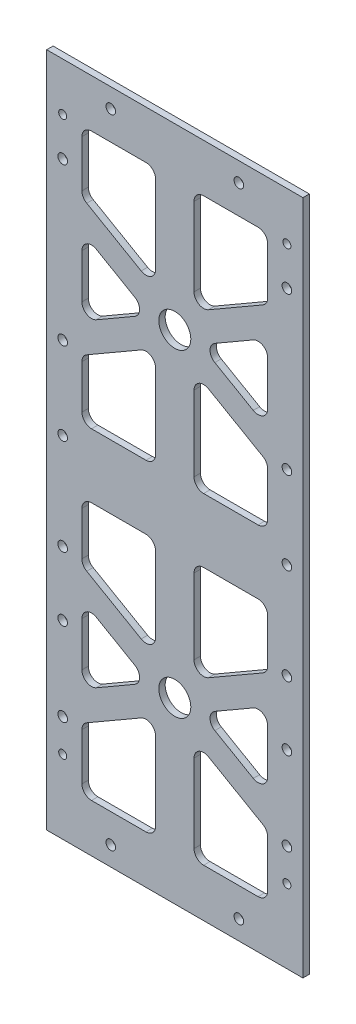
SolidWorks part; units mm, degrees
material "6061-T6 (SS)"
ref_plane "Front Plane" through (0, 0, 0) normal (0, 0, 1) x (1, 0, 0)
ref_plane "Top Plane" through (0, 0, 0) normal (0, 1, 0) x (1, 0, 0)
ref_plane "Right Plane" through (0, 0, 0) normal (1, 0, 0) x (0, 0, -1)
sketch "Sketch1" plane through (0, 0, 0) normal (0, 0, 1) x (1, 0, 0)
  line L1 (0, 0) -> (88, 0)
  line L2 (0, 0) -> (0, 211)
  line L3 (0, 211) -> (88, 211)
  line L4 (88, 0) -> (88, 211)
  dimension "D1" = 88
  dimension "D2" = 211
extrude "Boss-Extrude1" add sketch "Sketch1" along normal blind 2
sketch "Sketch2" plane through (0, 0, 2) normal (0, 0, 1) x (1, 0, 0)
  line L0 (0, 105.5) -> (88, 105.5) construction
  line L1 (0, 211) -> (0, 0) construction
  line L2 (88, 0) -> (88, 211) construction
  line L3 (44, 211) -> (44, 0) construction
  line L4 (88, 211) -> (0, 211) construction
  line L5 (0, 0) -> (88, 0) construction
  line L6 (0, 155.25) -> (88, 155.25) construction
  line L7 (0, 55.75) -> (88, 55.75) construction
  dimension "D1" = 55.75
  dimension "D2" = 55.75
sketch "Sketch3" plane through (0, 0, 2) normal (0, 0, 1) x (1, 0, 0)
  line L0 (0, 155.25) -> (88, 155.25) construction
  line L1 (38, 196) -> (38, 115.5)
  line L2 (0, 211) -> (0, 0) construction
  line L3 (15, 196) -> (73, 196)
  line L4 (15, 196) -> (15, 115.5)
  line L5 (15, 115.5) -> (73, 115.5)
  line L6 (73, 196) -> (73, 115.5)
  line L7 (88, 211) -> (0, 211) construction
  line L8 (88, 0) -> (88, 211) construction
  line L9 (0, 105.5) -> (88, 105.5) construction
  line L13 (73, 171.9932) -> (15, 138.5068) construction
  line L14 (15, 171.9932) -> (73, 138.5068) construction
  line L15 (73, 176.612) -> (15, 143.1256)
  line L16 (73, 167.3744) -> (15, 133.888)
  line L17 (15, 176.612) -> (73, 143.1256)
  line L18 (15, 167.3744) -> (73, 133.888)
  line L19 (50, 196) -> (50, 115.5)
  circle A0 centre (44, 155.25) radius 5
  dimension "D1" = 10
  dimension "D3" = 15
  dimension "D4" = 15
  dimension "D5" = 15
  dimension "D6" = 10
  dimension "D9" = 30
  dimension "D10" = 30
  dimension "D11" = 8
  dimension "D12" = 4
  dimension "D13" = 4
  dimension "D14" = 8
ref_plane "Plane1" through (0, 105.5, 0) normal (0, 1, 0) x (1, 0, 0)
extrude "Cut-Extrude2" cut sketch "Sketch3" against normal blind 2
sketch "Sketch4" plane through (0, 0, 2) normal (0, 0, 1) x (1, 0, 0)
  line L0 (0, 155.25) -> (88, 155.25) construction
  circle A0 centre (44, 155.25) radius 5
  dimension "D1" = 10
extrude "Cut-Extrude3" cut sketch "Sketch4" against normal through all
mirror "Mirror2" about plane through (0, 105.5, 0) normal (0, 1, 0) of "Cut-Extrude2", "Cut-Extrude3"
fillet "Fillet2" radius 3 44 edges at (73, 67.8744, 1) (73, 43.6256, 1) (52, 55.75, 1) (15, 15, 1) (15, 34.388, 1) (15, 143.1256, 1) (15, 167.3744, 1) (36, 155.25, 1) (15, 115.5, 1) (15, 133.888, 1) (73, 196, 1) (73, 115.5, 1) (73, 133.888, 1) (15, 196, 1) (15, 176.612, 1) (73, 167.3744, 1) (73, 143.1256, 1) (52, 155.25, 1) (73, 95.5, 1) (73, 77.112, 1) (73, 34.388, 1) (73, 15, 1) (15, 77.112, 1) (15, 95.5, 1) (15, 43.6256, 1) (15, 67.8744, 1) (36, 55.75, 1) (73, 176.612, 1) (50, 15, 1) (38, 15, 1) (38, 47.6671, 1) (50, 47.6671, 1) (38, 63.8329, 1) (38, 95.5, 1) (50, 63.8329, 1) (50, 95.5, 1) (38, 115.5, 1) (38, 147.1671, 1) (50, 147.1671, 1) (50, 115.5, 1) (38, 196, 1) (38, 163.3329, 1) (50, 163.3329, 1) (50, 196, 1)
sketch "Sketch23" plane through (0, 0, 2) normal (0, 0, 1) x (1, 0, 0)
  line L2 (88, 211) -> (88, 0)
  line L3 (86, 211) -> (86, 0)
  line L4 (86, 211) -> (88, 211)
  line L5 (86, 0) -> (88, 0)
  line L6 (2.1504, 211) -> (2.1504, 0)
  line L7 (2.1504, 211) -> (0, 211)
  line L8 (0, 211) -> (0, 0)
  line L9 (2.1504, 0) -> (0, 0)
  dimension "D1" = 2
extrude "Cut-Extrude5" cut sketch "Sketch23" against normal blind 10 contours L5 L2 L4 L3 | L6 L9 L8 L7
sketch "Sketch29" plane through (0, 0, 0) normal (0, 0, -1) x (-1, 0, 0)
  line L0 (-44, 0) -> (-44, 211)
  line L4 (-86, 105.5) -> (-2.1504, 105.5)
  line L5 (-86, 0) -> (-86, 211) construction
  line L6 (-2.1504, 0) -> (-2.1504, 211) construction
  line L16 (-4, 211) -> (1.9115, 211)
  line L17 (-4, 211) -> (-4, 0)
  line L18 (-4, 0) -> (1.9115, 0)
  line L19 (1.9115, 211) -> (1.9115, 0)
  line L20 (-84, 0) -> (-88.0365, 0)
  line L21 (-84, 0) -> (-84, 211)
  line L22 (-84, 211) -> (-88.0365, 211)
  line L23 (-88.0365, 0) -> (-88.0365, 211)
  point P0 (-44, 155.25)
  point P1 (-44, 217.1483)
  point P3 (-4, 155.25)
  point P4 (-4, 217.1483)
  point P5 (-84, 155.25)
  point P6 (-84, 217.1483)
  point P8 (-4, 105.5)
  point P22 (-84, 105.5)
  point P23 (-44, 105.5)
extrude "Cut-Extrude10" cut sketch "Sketch29" against normal blind 2
sketch "Sketch30" plane through (0, 0, 2) normal (0, 0, 1) x (1, 0, 0)
  line L0 (44, 211) -> (44, 0) construction
  line L1 (84, 211) -> (4, 211) construction
  line L2 (4, 0) -> (84, 0) construction
  line L3 (4, 211) -> (4, 0) construction
  point P8 (64, 6)
  point P9 (79, 23)
  point P10 (79, 33.2)
  point P11 (9, 33.2)
  point P13 (9, 196)
  point P14 (9, 184)
  point P15 (9, 135)
  point P16 (9, 109.2)
  point P18 (9, 79.2)
  point P19 (9, 59.2)
  point P20 (79, 59.2)
  point P21 (9, 23)
  point P23 (24, 205)
  point P25 (79, 79.2)
  point P26 (79, 109.2)
  point P27 (24, 6)
  point P29 (79, 135)
  point P30 (79, 184)
  point P31 (79, 196)
  point P32 (64, 205)
  dimension "D1" = 20
  dimension "D2" = 6
  dimension "D3" = 5
  dimension "D4" = 15
  dimension "D5" = 27
  dimension "D6" = 76
  dimension "D7" = 101.8
  dimension "D8" = 131.8
  dimension "D9" = 151.8
  dimension "D10" = 5
  dimension "D11" = 188
  dimension "D12" = 205
  dimension "D13" = 20
  dimension "D14" = 5
  dimension "D15" = 5
  dimension "D16" = 5
  dimension "D17" = 5
  dimension "D18" = 5
  dimension "D19" = 5
  dimension "D20" = 177.8
hole_wizard "Ø3.0mm Dowel Hole1" positions "Sketch31" profile "Sketch32" hole size "Ø3.0" standard "ANSI Metric" end condition through all
sketch "Sketch31" plane through (0, 0, 2) normal (0, 0, 1) x (1, 0, 0)
  point P0 (24, 205)
  point P3 (64, 205)
  point P6 (9, 184)
  point P9 (79, 184)
  point P12 (9, 135)
  point P15 (79, 135)
  point P18 (79, 109.2)
  point P21 (9, 109.2)
  point P24 (9, 79.2)
  point P27 (79, 79.2)
  point P30 (79, 59.2)
  point P33 (9, 59.2)
  point P36 (9, 33.2)
  point P39 (79, 33.2)
  point P42 (64, 6)
  point P45 (24, 6)
sketch "Sketch32" plane through (24, 205, 2) normal (1, 0, 0) x (0, -1, 0)
  line L0 (0, 0) -> (0, 2)
  line L1 (0, 2) -> (1.5, 2)
  line L2 (1.5, 2) -> (1.5, 0)
  line L5 (1.5, 0) -> (0, 0)
  line L11 (0, -6.35) -> (0, 107.95) construction
  dimension "Thru Hole Dia." = 3
  dimension "Thru Hole Depth" = 2
hole_wizard "Tap Drill for M3x0.5 Tap1" positions "Sketch33" profile "Sketch34" hole size "M3x0.5" standard "ANSI Metric" end condition through all
sketch "Sketch33" plane through (0, 0, 2) normal (0, 0, 1) x (1, 0, 0)
  point P0 (9, 23)
  point P3 (79, 23)
  point P6 (9, 196)
  point P9 (79, 196)
sketch "Sketch34" plane through (9, 23, 2) normal (1, 0, 0) x (0, -1, 0)
  line L0 (0, 0) -> (0, 2)
  line L1 (0, 2) -> (1.25, 2)
  line L2 (1.25, 2) -> (1.25, 0)
  line L5 (1.25, 0) -> (0, 0)
  line L11 (0, -6.35) -> (0, 107.95) construction
  dimension "Thru Hole Dia." = 2.5
  dimension "Thru Hole Depth" = 2
equation "\"stack_house_hole_distance\"=15"
equation "\"battery_top_clearance\"=15"
equation "\"coils_top_clearance\"=10"
